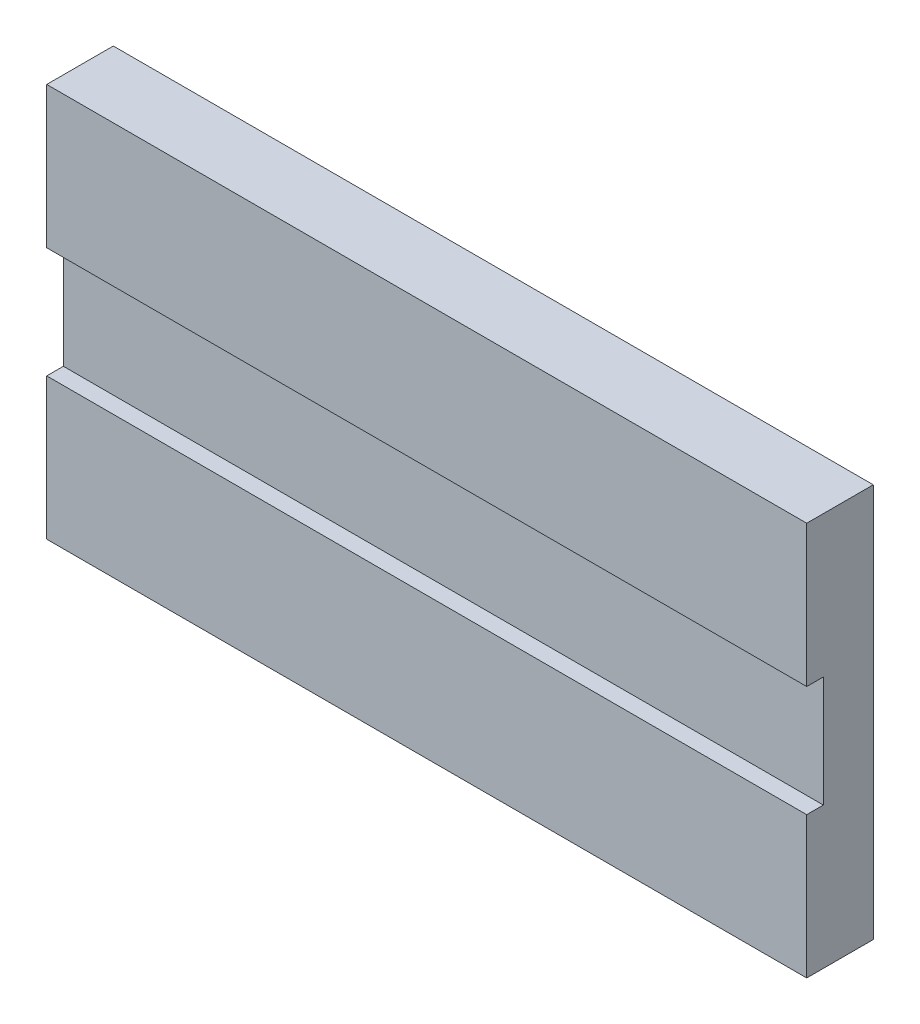
SolidWorks part; units mm, degrees
ref_plane "Plan de face" through (0, 0, 0) normal (0, 0, 1) x (1, 0, 0)
ref_plane "Plan de dessus" through (0, 0, 0) normal (0, 1, 0) x (1, 0, 0)
ref_plane "Plan de droite" through (0, 0, 0) normal (1, 0, 0) x (0, 0, -1)
sketch "Esquisse1" plane through (0, 0, 0) normal (0, 0, 1) x (1, 0, 0)
  line L0 (0, 0) -> (137, 0)
  line L1 (137, 0) -> (137, -71)
  line L2 (137, -71) -> (0, -71)
  line L3 (0, -71) -> (0, 0)
extrude "Extrusion1" add sketch "Esquisse1" along normal blind 12
sketch "Esquisse2" plane through (137, 0, 0) normal (1, 0, 0) x (0, 0, -1)
  line L0 (-6, -71) -> (-6, -56.5258) construction
  line L6 (-12, -71) -> (0, -71) construction
  line L7 (-12, -45.5) -> (-9, -45.5)
  line L8 (-12, -25.5) -> (-12, -45.5)
  line L9 (-9, -25.5) -> (-12, -25.5)
  line L10 (-9, -45.5) -> (-9, -25.5)
extrude "Extrusion2" cut sketch "Esquisse2" against normal through all
